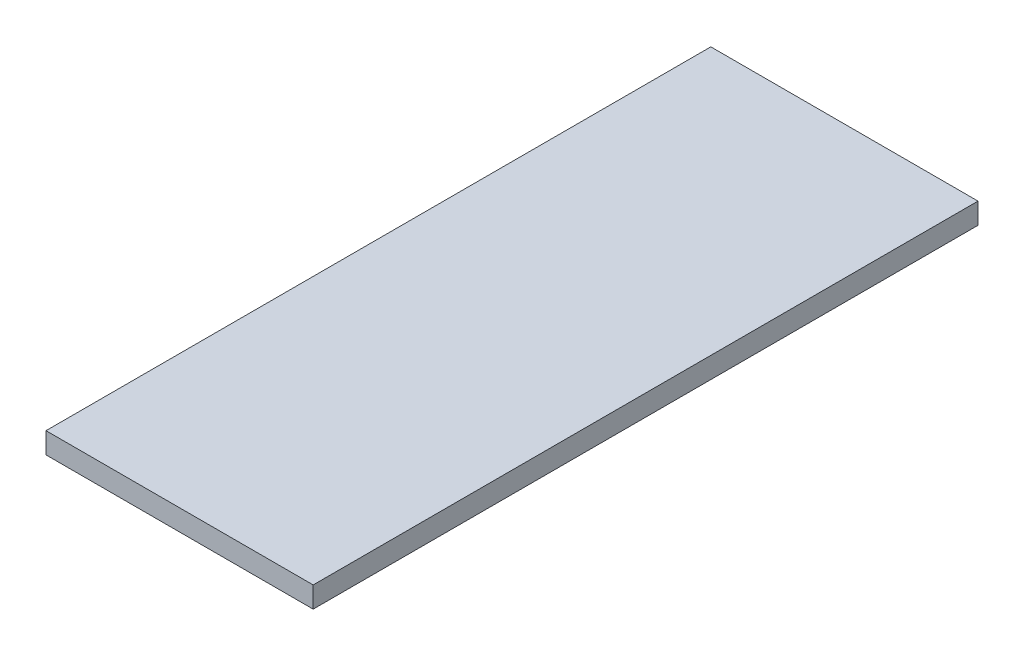
SolidWorks part; units mm, degrees
ref_plane "Front Plane" through (0, 0, 0) normal (0, 0, 1) x (1, 0, 0)
ref_plane "Top Plane" through (0, 0, 0) normal (0, 1, 0) x (1, 0, 0)
ref_plane "Right Plane" through (0, 0, 0) normal (1, 0, 0) x (0, 0, -1)
sketch "Sketch1" plane through (0, 0, 0) normal (0, 0, 1) x (1, 0, 0)
  line L1 (-700, 55) -> (700, 55)
  line L2 (-700, 55) -> (-700, -55)
  line L3 (-700, -55) -> (700, -55)
  line L4 (700, 55) -> (700, -55)
  line L5 (-700, 55) -> (700, -55) construction
  line L6 (-700, -55) -> (700, 55) construction
  point P0 (0, 0)
  dimension "D1" = 1400
  dimension "D2" = 110
extrude "Boss-Extrude1" add sketch "Sketch1" along normal blind 3483.5
